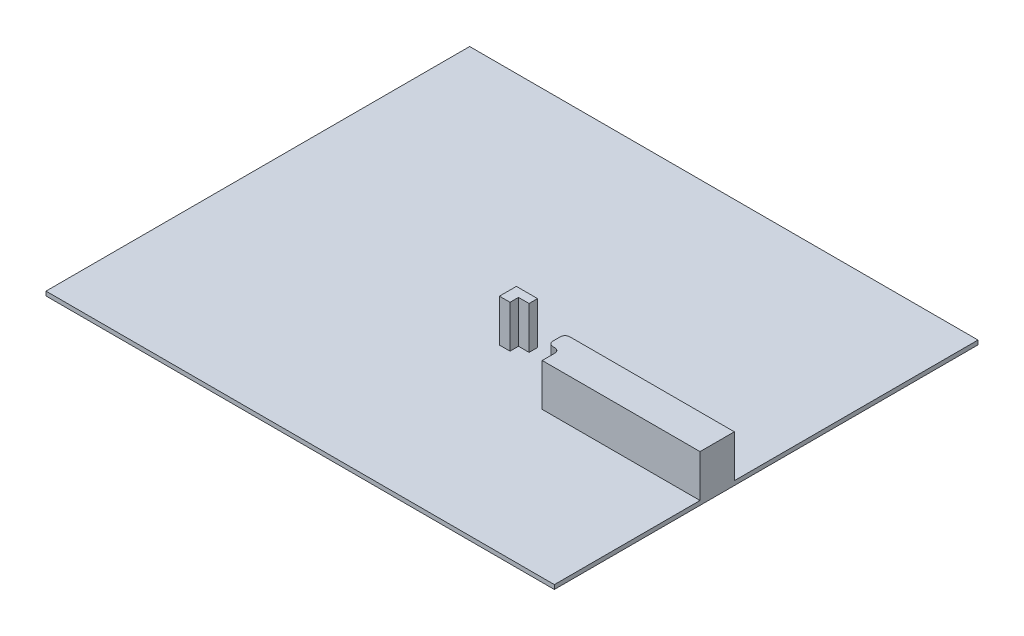
SolidWorks part; units mm, degrees
material "AISI 1015 Steel, Cold Drawn (SS)"
ref_plane "Front Plane" through (0, 0, 0) normal (0, 0, 1) x (1, 0, 0)
ref_plane "Top Plane" through (0, 0, 0) normal (0, 1, 0) x (1, 0, 0)
ref_plane "Right Plane" through (0, 0, 0) normal (1, 0, 0) x (0, 0, -1)
sketch "Sketch2" plane through (0, 0, 0) normal (0, 1, 0) x (1, 0, 0)
  line L1 (-600, -500) -> (600, -500)
  line L2 (-600, -500) -> (-600, 500)
  line L3 (-600, 500) -> (600, 500)
  line L4 (600, -500) -> (600, 500)
  line L5 (-600, -500) -> (600, 500) construction
  line L6 (-600, 500) -> (600, -500) construction
  point P0 (0, 0)
  dimension "D1" = 1200
  dimension "D2" = 1000
extrude "Boss-Extrude1" add sketch "Sketch2" along normal blind 10
sketch "Sketch4" plane through (0, 10, 0) normal (0, 1, 0) x (1, 0, 0)
  line L0 (211.5003, -115.1731) -> (216.5003, -115.1731)
  line L1 (600, -75.1731) -> (211.5003, -75.1731)
  line L2 (600, -75.1731) -> (600, -95.1731)
  line L3 (227.5003, -156.1731) -> (600, -156.1731)
  line L4 (200.5003, -86.1731) -> (200.5003, -104.1731)
  line L5 (600, -156.1731) -> (600, -95.1731)
  line L7 (600, -500) -> (600, 500) construction
  line L9 (227.5003, -126.1731) -> (227.5003, -156.1731)
  arc A0 (227.5003, -126.1731) -> (216.5003, -115.1731) centre (216.5003, -126.1731) ccw
  arc A1 (211.5003, -75.1731) -> (200.5003, -86.1731) centre (211.5003, -86.1731) ccw
  arc A2 (200.5003, -104.1731) -> (211.5003, -115.1731) centre (211.5003, -104.1731) ccw
  point P13 (200.5003, -75.1731)
  point P16 (200.5003, -115.1731)
  dimension "D6" = 11
  dimension "D7" = 11
  dimension "D3" = 11
  dimension "D1" = 20
  dimension "D2" = 400
  dimension "D4" = 30
  dimension "D5" = 40
extrude "Boss-Extrude2" add sketch "Sketch4" along normal blind 100
sketch "Sketch5" plane through (0, 10, 0) normal (0, 1, 0) x (1, 0, 0)
  line L1 (95.5003, -55.1731) -> (95.5003, -35.1731)
  line L2 (95.5003, -35.1731) -> (45.5003, -35.1731)
  line L3 (45.5003, -35.1731) -> (45.5003, -75.1731)
  line L4 (45.5003, -75.1731) -> (70.5003, -75.1731)
  line L6 (95.5003, -55.1731) -> (70.5003, -55.1731)
  line L7 (70.5003, -55.1731) -> (70.5003, -75.1731)
  dimension "D2" = 50
  dimension "D3" = 40
  dimension "D4" = 25
extrude "Boss-Extrude3" add sketch "Sketch5" along normal blind 100
